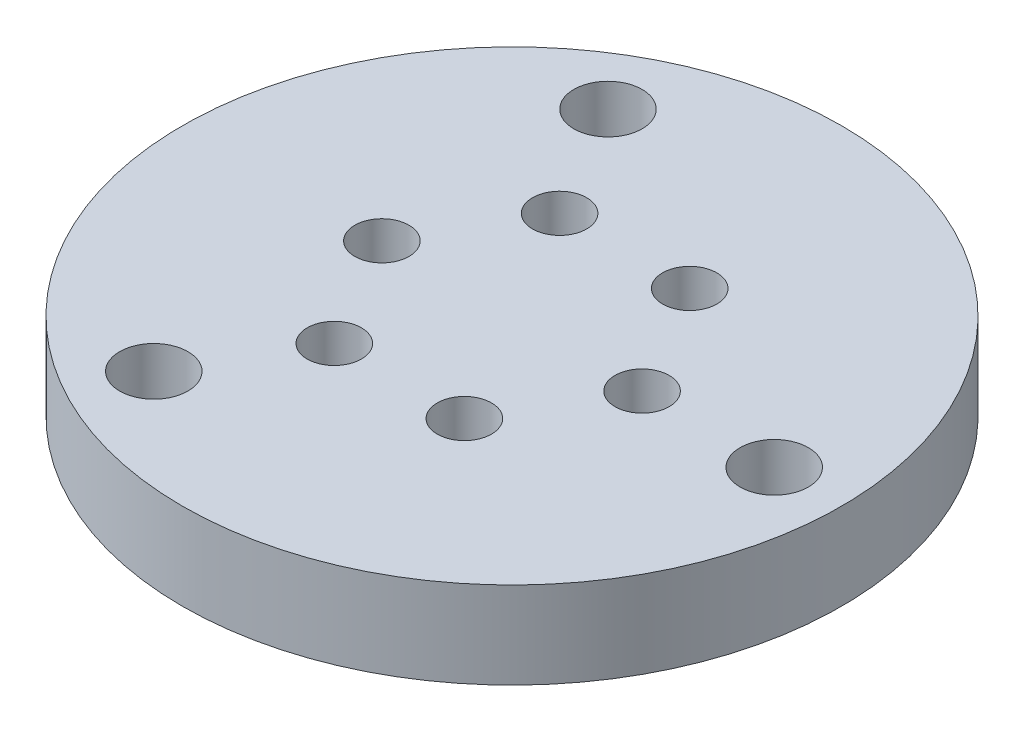
SolidWorks part; units mm, degrees
material "ABS"
ref_plane "Front Plane" through (0, 0, 0) normal (0, 0, 1) x (1, 0, 0)
ref_plane "Top Plane" through (0, 0, 0) normal (0, 1, 0) x (1, 0, 0)
ref_plane "Right Plane" through (0, 0, 0) normal (1, 0, 0) x (0, 0, -1)
sketch "Sketch1" plane through (0, 0, 0) normal (0, 1, 0) x (1, 0, 0)
  line L0 (13, 0) -> (25.4, 0) construction
  line L2 (19.2, 0) -> (9.6, 16.6277) construction
  line L3 (9.6, 16.6277) -> (-9.6, 16.6277) construction
  line L4 (-9.6, 16.6277) -> (-19.2, 0) construction
  line L5 (-19.2, 0) -> (-9.6, -16.6277) construction
  line L6 (-9.6, -16.6277) -> (9.6, -16.6277) construction
  line L7 (9.6, -16.6277) -> (19.2, 0) construction
  circle A0 centre (0, 0) radius 24.13
  circle A1 centre (0, 0) radius 25.4 construction
  circle A2 centre (0, 0) radius 13 construction
  circle A3 centre (19.2, 0) radius 2.5
  circle A4 centre (0, 0) radius 16.6277 construction
  circle A5 centre (-9.6, 16.6277) radius 2.5
  circle A6 centre (-9.6, -16.6277) radius 2.5
  dimension "D1" = 48.26
  dimension "D2" = 50.8
  dimension "D3" = 26
  dimension "D4" = 5
  dimension "D5" = 5
  dimension "D6" = 5
extrude "Boss-Extrude1" add sketch "Sketch1" along normal blind 6.35
sketch "Sketch2" plane through (0, 6.35, 0) normal (0, 1, 0) x (1, 0, 0)
  line L1 (9.525, 0) -> (4.7625, 8.2489)
  line L2 (4.7625, 8.2489) -> (-4.7625, 8.2489)
  line L3 (-4.7625, 8.2489) -> (-9.525, 0)
  line L4 (-9.525, 0) -> (-4.7625, -8.2489)
  line L5 (-4.7625, -8.2489) -> (4.7625, -8.2489)
  line L6 (4.7625, -8.2489) -> (9.525, 0)
  circle A0 centre (0, 0) radius 8.2489 construction
  dimension "D1" = 9.525
sketch "Sketch3" plane through (0, 6.35, 0) normal (0, 1, 0) x (1, 0, 0)
  circle A0 centre (0, 0) radius 6.1
  circle A1 centre (0, 0) radius 8.2489 construction
  circle A2 centre (0, 0) radius 8.2489
  dimension "D1" = 12.2
hole_wizard "5/32 (0.15625) Diameter Hole1" positions "Sketch4" profile "Sketch5" hole size "5/32" standard "ANSI Inch" end condition through all
sketch "Sketch4" plane through (0, 6.35, 0) normal (0, 1, 0) x (1, 0, 0)
  point P0 (4.7625, 8.2489)
  point P3 (-4.7625, 8.2489)
  point P6 (-9.525, 0)
  point P9 (-4.7625, -8.2489)
  point P12 (4.7625, -8.2489)
  point P15 (9.525, 0)
sketch "Sketch5" plane through (4.7625, 6.35, -8.2489) normal (1, 0, 0) x (0, 0, 1)
  line L0 (0, 0) -> (0, 6.35)
  line L1 (0, 6.35) -> (1.9844, 6.35)
  line L2 (1.9844, 6.35) -> (1.9844, 0)
  line L5 (1.9844, 0) -> (0, 0)
  line L11 (0, -6.35) -> (0, 107.95) construction
  dimension "Thru Hole Dia." = 3.9688
  dimension "Thru Hole Depth" = 6.35
